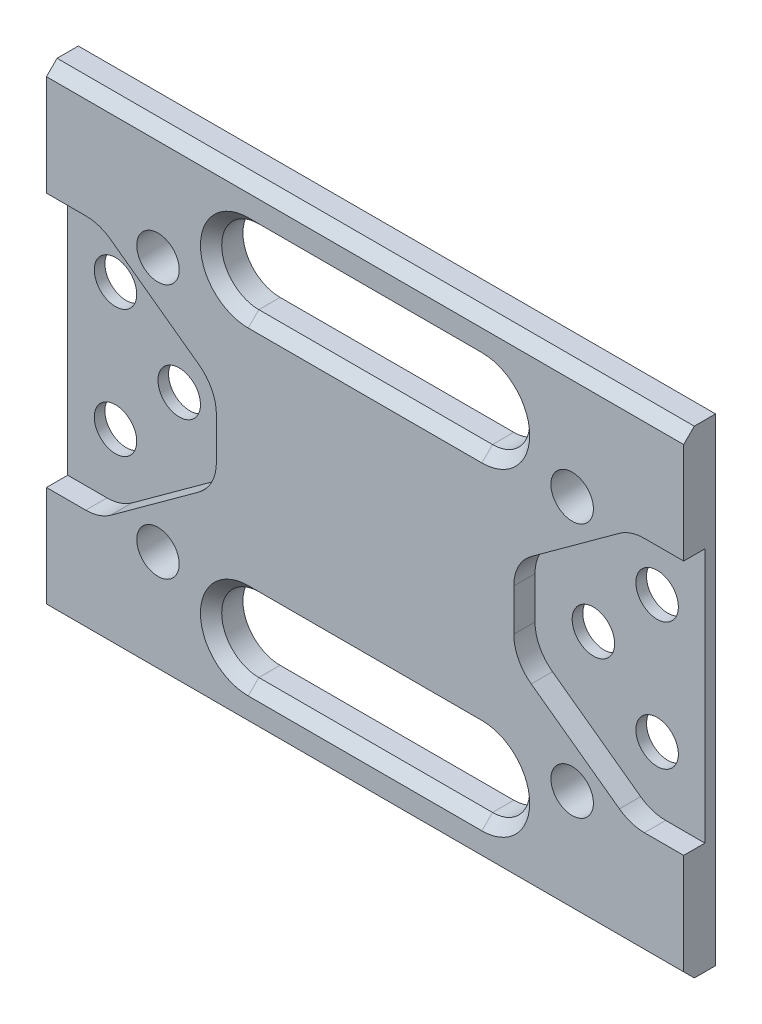
SolidWorks part; units mm, degrees
material "1060 Alloy"
ref_plane "Front Plane" through (0, 0, 0) normal (0, 0, 1) x (1, 0, 0)
ref_plane "Top Plane" through (0, 0, 0) normal (0, 1, 0) x (1, 0, 0)
ref_plane "Right Plane" through (0, 0, 0) normal (1, 0, 0) x (0, 0, -1)
sketch "Sketch1" plane through (0, 0, 0) normal (0, 0, 1) x (1, 0, 0)
  line L1 (-30, 22.5) -> (30, 22.5)
  line L2 (-30, 22.5) -> (-30, -22.5)
  line L3 (-30, -22.5) -> (30, -22.5)
  line L4 (30, 22.5) -> (30, -22.5)
  line L5 (-30, 22.5) -> (30, -22.5) construction
  line L6 (-30, -22.5) -> (30, 22.5) construction
  dimension "D1" = 60
  dimension "D2" = 45
extrude "Boss-Extrude1" add sketch "Sketch1" along normal blind 3
sketch "Sketch2" plane through (0, 0, 0) normal (0, 0, -1) x (-1, 0, 0)
  line L0 (0, 0) -> (30, 0) construction
  line L1 (30, 22.5) -> (30, -22.5) construction
  circle A0 centre (19.5, 0) radius 2
  circle A1 centre (25.5, 6) radius 2
  circle A2 centre (25.5, -6) radius 2
  circle A3 centre (19.5, -12) radius 2
  circle A4 centre (19.5, 12) radius 2
  dimension "D1" = 4
  dimension "D2" = 10.5
  dimension "D3" = 12
  dimension "D4" = 6
  dimension "D5" = 4.5
  dimension "D6" = 12
  dimension "D7" = 12
extrude "Cut-Extrude1" cut sketch "Sketch2" against normal blind 5
ref_plane "Plane1" through (0, 0, 0) normal (1, 0, 0) x (0, 0, -1)
sketch "Sketch3" plane through (0, 0, 3) normal (0, 0, 1) x (1, 0, 0)
  line L0 (0, 0) -> (-10, 0) construction
  line L1 (-10, 0) -> (-10, 14.5) construction
  line L2 (30, 22.5) -> (-30, 22.5) construction
  line L3 (-8, 14.5) -> (-8, 6.5)
  line L5 (-12, 6.5) -> (-12, 14.5)
  arc A0 (-12, 6.5) -> (-8, 6.5) centre (-10, 6.5) ccw
  arc A1 (-8, 14.5) -> (-12, 14.5) centre (-10, 14.5) ccw
  dimension "D1" = 4
  dimension "D2" = 4
  dimension "D3" = 10
  dimension "D4" = 8
  dimension "D5" = 8
ref_plane "Plane3" through (0, 0, 0) normal (0, -1, 0) x (-1, 0, 0)
sketch "Sketch8" plane through (0, 0, 3) normal (0, 0, 1) x (1, 0, 0)
  line L0 (-14, 4) -> (-14, -4)
  line L1 (-14, -4) -> (-25, -12)
  line L2 (-25, -12) -> (-30, -12)
  line L3 (-30, 22.5) -> (-30, -22.5) construction
  line L4 (-14, 4) -> (-25, 12)
  line L5 (-25, 12) -> (-30, 12)
  line L6 (-30, 12) -> (-30, -12)
  line L7 (0, 0) -> (-14, 0) construction
  line L8 (-14, 0) -> (-30, 0) construction
  dimension "D1" = 8
  dimension "D3" = 8
  dimension "D4" = 8
  dimension "D5" = 5
  dimension "D6" = 5
  dimension "D7" = 16
extrude "Cut-Extrude5" cut sketch "Sketch8" against normal blind 2
sketch "Sketch7" plane through (0, 0, 3) normal (0, 0, 1) x (1, 0, 0)
  line L6 (-11, -18.5) -> (9, -18.5)
  line L7 (9, -18.5) -> (9, -11.5)
  line L8 (9, -11.5) -> (-11, -11.5)
  line L10 (-11, 11.5) -> (9, 11.5)
  line L11 (9, 11.5) -> (9, 18.5)
  line L12 (9, 18.5) -> (-11, 18.5)
  arc A2 (-11, 18.5) -> (-11, 11.5) centre (-11, 15) ccw
  arc A3 (-11, -11.5) -> (-11, -18.5) centre (-11, -15) ccw
  dimension "D1" = 3.5
  dimension "D2" = 3.5
  dimension "D3" = 11.5
  dimension "D4" = 11.5
  dimension "D5" = 11
  dimension "D6" = 11
  dimension "D7" = 20
extrude "Cut-Extrude4" cut sketch "Sketch7" against normal blind 5
chamfer "Chamfer2" distance 1 angle 45 2 edges at (0, 22.5, 3) (0, -22.5, 3)
fillet "Fillet1" radius 4 4 edges at (-14, -4, 2) (-14, 4, 2) (-25, 12, 2) (-25, -12, 2)
mirror "Mirror4" about plane through (0, 0, 0) normal (1, 0, 0) of "Fillet1", "Cut-Extrude1", "Cut-Extrude4", "Cut-Extrude5"
chamfer "Chamfer1" distance 1 angle 45 8 edges at (0, -18.5, 3) (14.5, -15, 3) (-14.5, -15, 3) (0, -11.5, 3) (0, 18.5, 3) (-14.5, 15, 3) (14.5, 15, 3) (0, 11.5, 3)
